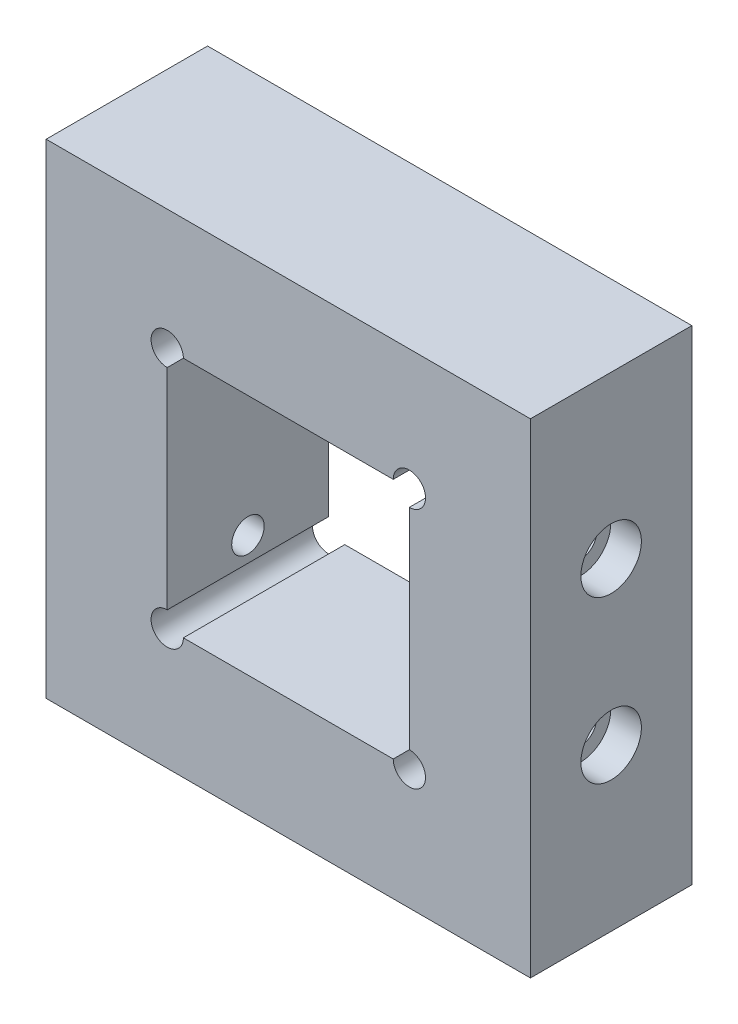
SolidWorks part; units mm, degrees
material "Copper"
ref_plane "Front Plane" through (0, 0, 0) normal (0, 0, 1) x (1, 0, 0)
ref_plane "Top Plane" through (0, 0, 0) normal (0, 1, 0) x (1, 0, 0)
ref_plane "Right Plane" through (0, 0, 0) normal (1, 0, 0) x (0, 0, -1)
sketch "Sketch1" plane through (0, 0, 0) normal (0, 0, 1) x (1, 0, 0)
  line L1 (-38.1, 38.1) -> (38.1, 38.1)
  line L2 (-38.1, 38.1) -> (-38.1, -38.1)
  line L3 (-38.1, -38.1) -> (38.1, -38.1)
  line L4 (38.1, 38.1) -> (38.1, -38.1)
  dimension "D1" = 38.1
  dimension "D2" = 38.1
  dimension "D3" = 38.1
  dimension "D4" = 38.1
extrude "Boss-Extrude1" add sketch "Sketch1" along normal mid plane 25.4
sketch "Sketch2" plane through (0, 0, 12.7) normal (0, 0, 1) x (1, 0, 0)
  line L1 (-19.05, 19.05) -> (19.05, 19.05)
  line L2 (-19.05, 19.05) -> (-19.05, -19.05)
  line L3 (-19.05, -19.05) -> (19.05, -19.05)
  line L4 (19.05, 19.05) -> (19.05, -19.05)
  dimension "D1" = 19.05
  dimension "D2" = 19.05
  dimension "D3" = 19.05
  dimension "D4" = 19.05
extrude "Cut-Extrude1" cut sketch "Sketch2" against normal through all
hole_wizard "CBORE for #10 Socket Head Cap Screw1" positions "Sketch4" profile "Sketch3" counterbore size "#10" standard "ANSI Inch"
sketch "Sketch4" plane through (38.1, 0, 0) normal (1, 0, 0) x (0, 0, -1)
  point P0 (0, 12.7)
  point P2 (0, -12.7)
  dimension "D1" = 12.7
  dimension "D2" = 12.7
sketch "Sketch3" plane through (38.1, 12.7, 0) normal (0, 1, 0) x (0, 0, -1)
  line L0 (0, 0) -> (0, 76.2)
  line L1 (0, 76.2) -> (2.5527, 76.2)
  line L3 (2.5527, 76.2) -> (2.5527, 4.826)
  line L4 (2.5527, 4.826) -> (4.7625, 4.826)
  line L5 (4.7625, 4.826) -> (4.7625, 0)
  line L7 (4.7625, 0) -> (0, 0)
  line L11 (0, -6.35) -> (0, 107.95) construction
  dimension "Thru Hole Dia." = 5.1054
  dimension "Thru Hole Depth" = 76.2
  dimension "C'Bore Dia." = 9.525
  dimension "C'Bore Depth" = 4.826
sketch "Sketch5" plane through (0, 0, 12.7) normal (0, 0, 1) x (1, 0, 0)
  circle A0 centre (19.05, 19.05) radius 2.54
  circle A1 centre (19.05, -19.05) radius 2.54
extrude "Cut-Extrude2" cut sketch "Sketch5" against normal up to next
mirror "Mirror1" about plane through (0, 0, 0) normal (1, 0, 0) of "Cut-Extrude2", "CBORE for #10 Socket Head Cap Screw1"
